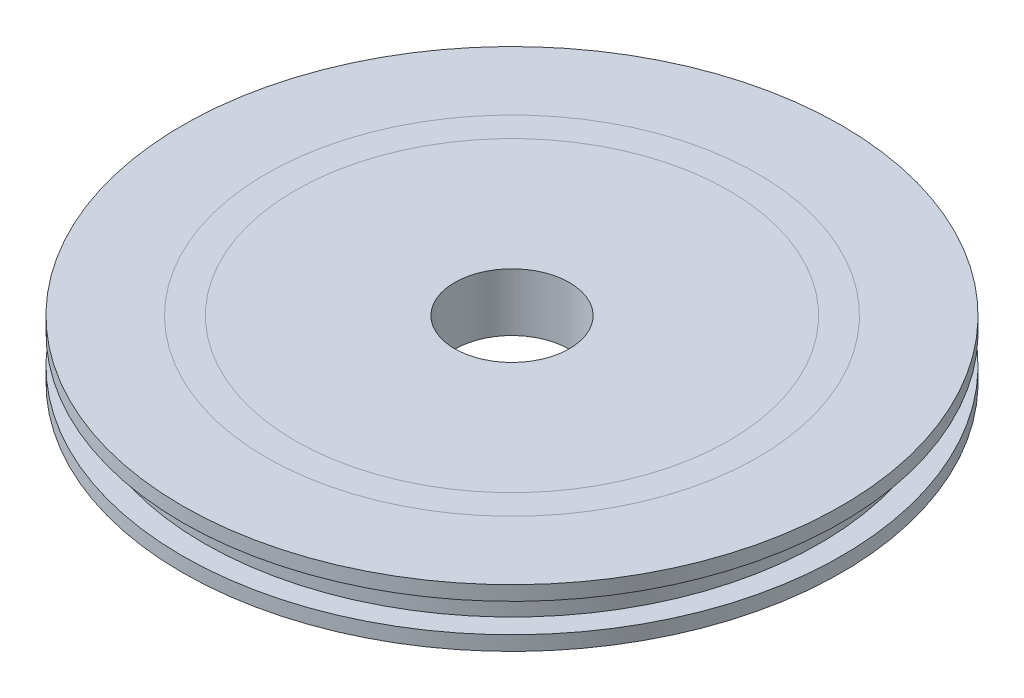
SolidWorks part; units mm, degrees
material "6061-T6 (SS)"
ref_plane "X-Y Datum" through (0, 0, 0) normal (0, 0, 1) x (1, 0, 0)
ref_plane "X-Z Datum" through (0, 0, 0) normal (0, 1, 0) x (1, 0, 0)
ref_plane "Y-Z Datum" through (0, 0, 0) normal (1, 0, 0) x (0, 0, -1)
sketch "Sketch1" plane through (0, 0, 0) normal (1, 0, 0) x (0, 0, -1)
  line L0 (0, 0) -> (0, -32027.2037) construction
  line L1 (0, 0) -> (0, -5.08)
  line L2 (0, -5.08) -> (-28.956, -5.08)
  line L3 (-28.956, -5.08) -> (-28.956, -3.81)
  line L4 (-28.956, -3.81) -> (-27.051, -3.81)
  line L5 (-27.051, -3.81) -> (-27.051, -1.27)
  line L6 (-27.051, -1.27) -> (-28.956, -1.27)
  line L7 (-28.956, -1.27) -> (-28.956, 0)
  line L8 (-28.956, 0) -> (0, 0)
  dimension "D1" = 57.912
  dimension "D2" = 5.08
  dimension "D3" = 2.54
  dimension "D5" = 54.102
revolve "Revolve1" add sketch "Sketch1" angle 360 about L0
sketch "Sketch2" plane through (0, 0, 0) normal (0, 1, 0) x (1, 0, 0)
  circle A0 centre (0, 0) radius 19.05
  dimension "D1" = 38.1
split line "Split Line1"
sketch "Sketch3" plane through (0, 0, 0) normal (0, 1, 0) x (1, 0, 0)
  circle A0 centre (0, 0) radius 21.59
  dimension "D1" = 43.18
split line "Split Line2"
hole_wizard "Ø10.0mm Dowel Hole1" positions "Sketch4" profile "Sketch5" hole size "Ø10.0" standard "ANSI Metric"
sketch "Sketch4" plane through (0, 0, 0) normal (0, 1, 0) x (1, 0, 0)
  point P0 (0, 0)
sketch "Sketch5" plane through (0, 0, 0) normal (1, 0, 0) x (0, 0, 1)
  line L0 (0, 0) -> (0, 5.08)
  line L1 (0, 5.08) -> (5, 5.08)
  line L2 (5, 5.08) -> (5, 0)
  line L5 (5, 0) -> (0, 0)
  line L11 (0, -6.35) -> (0, 107.95) construction
  dimension "Thru Hole Dia." = 10
  dimension "Thru Hole Depth" = 5.08
sketch "Sketch6" plane through (0, -5.08, 0) normal (0, -1, 0) x (1, 0, 0)
  circle A0 centre (0, 0) radius 5.0419
  dimension "D1" = 10.0838
extrude "Cut-Extrude1" cut sketch "Sketch6" against normal through all
